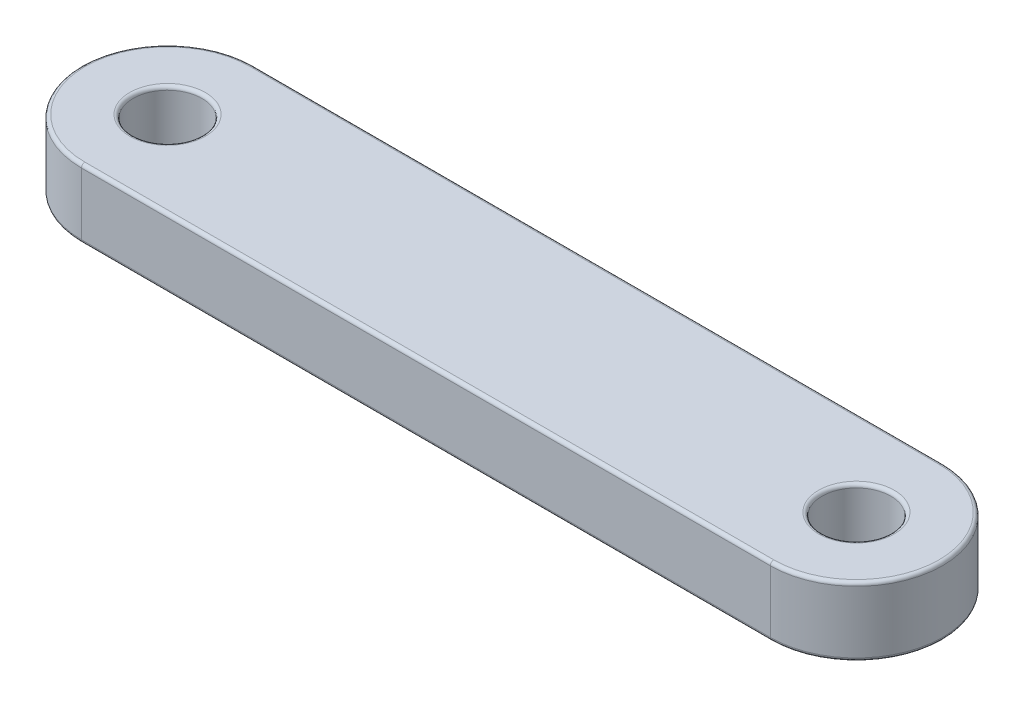
SolidWorks part; units mm, degrees
material "Alloy Steel"
ref_plane "Front Plane" through (0, 0, 0) normal (0, 0, 1) x (1, 0, 0)
ref_plane "Top Plane" through (0, 0, 0) normal (0, 1, 0) x (1, 0, 0)
ref_plane "Right Plane" through (0, 0, 0) normal (1, 0, 0) x (0, 0, -1)
sketch "Sketch1" plane through (0, 0, 0) normal (0, 1, 0) x (1, 0, 0)
  line L0 (-100, 0) -> (100, 0) construction
  line L1 (-100, 25) -> (100, 25)
  line L2 (-100, -25) -> (100, -25)
  line L3 (0, 0) -> (0, 241.5958) construction
  arc A0 (-100, 25) -> (-100, -25) centre (-100, 0) ccw
  arc A1 (100, -25) -> (100, 25) centre (100, 0) ccw
  circle A2 centre (-100, 0) radius 10
  circle A3 centre (100, 0) radius 10
  point P2 (0, 0)
  dimension "D2" = 20
  dimension "D3" = 50
  dimension "D1" = 200
extrude "Boss-Extrude1" add sketch "Sketch1" along normal blind 20
fillet "Fillet1" radius 1 12 edges at (100, 0, -10) (-100, 0, 10) (0, 0, 25) (125, 0, 0) (0, 0, -25) (-125, 0, 0) (100, 20, -10) (0, 20, -25) (125, 20, 0) (0, 20, 25) (-125, 20, 0) (-100, 20, 10)
scale "Scale1" scale about centroid uniform scaling yes scale factor 0.125
